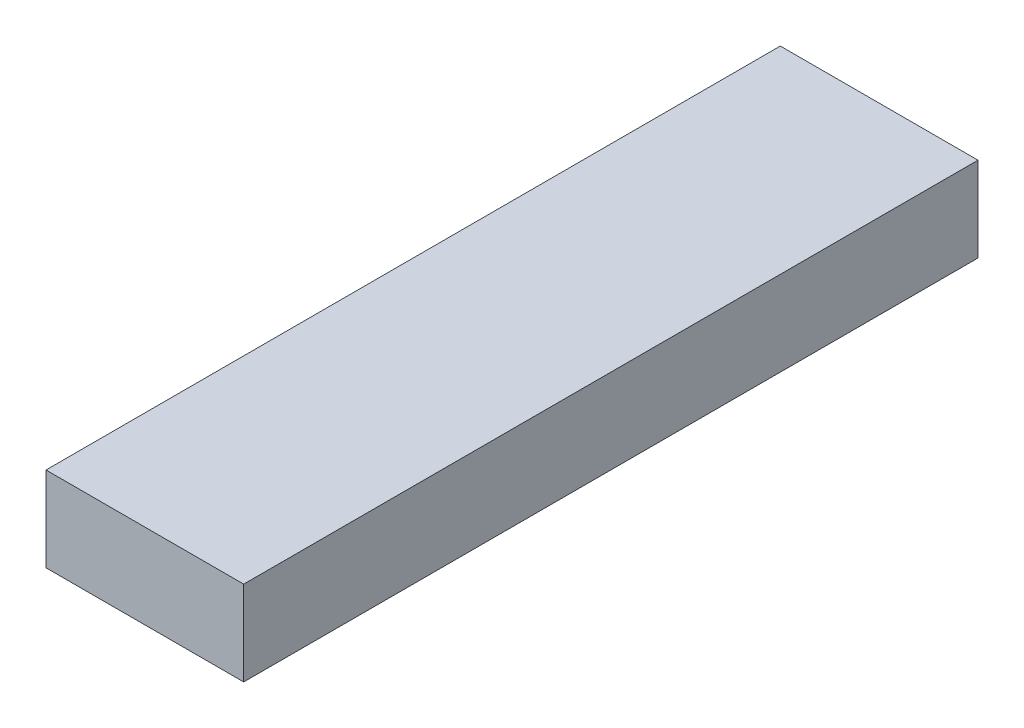
SolidWorks part; units mm, degrees
material "Pine"
ref_plane "Front Plane" through (0, 0, 0) normal (0, 0, 1) x (1, 0, 0)
ref_plane "Top Plane" through (0, 0, 0) normal (0, 1, 0) x (1, 0, 0)
ref_plane "Right Plane" through (0, 0, 0) normal (1, 0, 0) x (0, 0, -1)
sketch "Sketch1" plane through (0, 0, 0) normal (0, 0, 1) x (1, 0, 0)
  line L1 (80.1838, 99.226) -> (169.0838, 99.226)
  line L2 (80.1838, 99.226) -> (80.1838, 61.126)
  line L3 (80.1838, 61.126) -> (169.0838, 61.126)
  line L4 (169.0838, 99.226) -> (169.0838, 61.126)
  dimension "D1" = 88.9
  dimension "D2" = 38.1
extrude "Boss-Extrude1" add sketch "Sketch1" along normal blind 330.2
